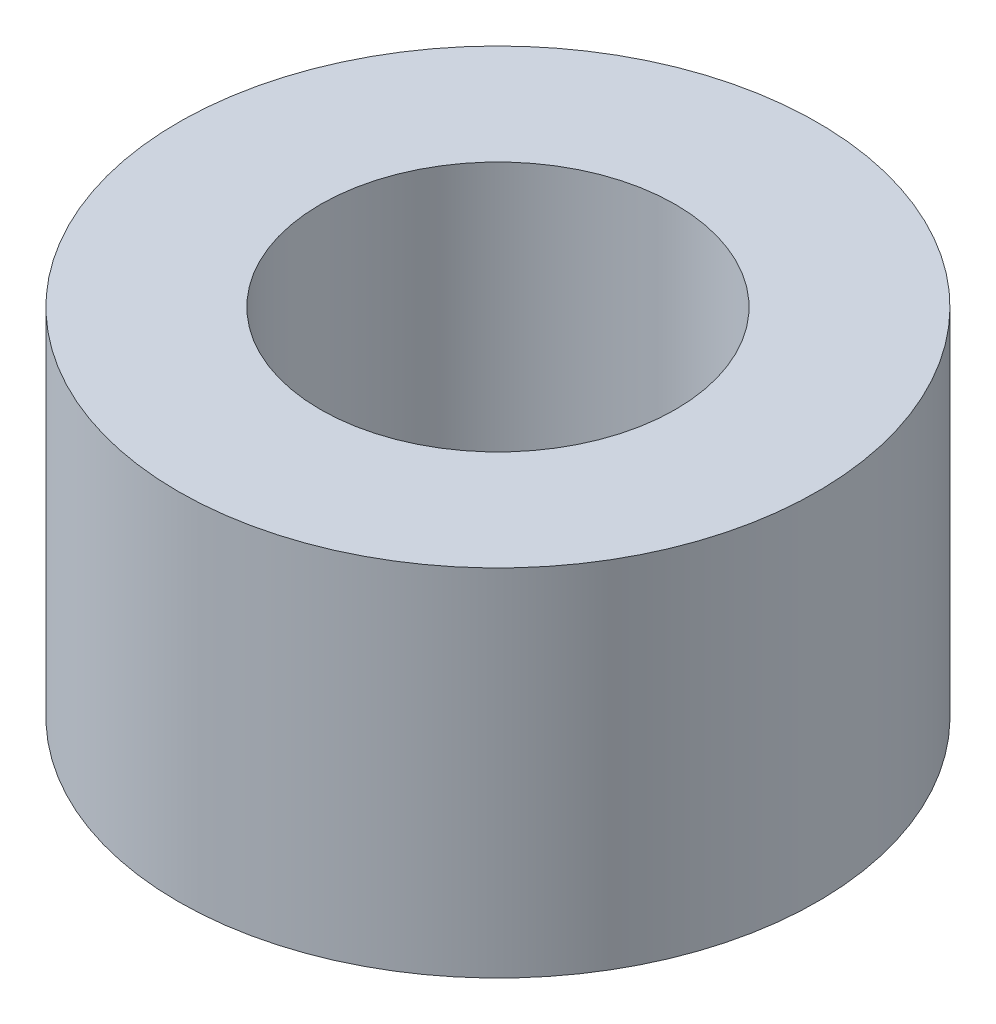
SolidWorks part; units mm, degrees
ref_plane "Front" through (0, 0, 0) normal (0, 0, 1) x (1, 0, 0)
ref_plane "Top" through (0, 0, 0) normal (0, 1, 0) x (1, 0, 0)
ref_plane "Right" through (0, 0, 0) normal (1, 0, 0) x (0, 0, -1)
sketch "Sketch1" plane through (0, 0, 0) normal (0, 1, 0) x (1, 0, 0)
  circle A0 centre (0, 0) radius 2.25
  circle A1 centre (0, 0) radius 1.25
  dimension "D1" = 2.5
  dimension "D2" = 1
extrude "Boss-Extrude1" add sketch "Sketch1" along normal blind 2.5
